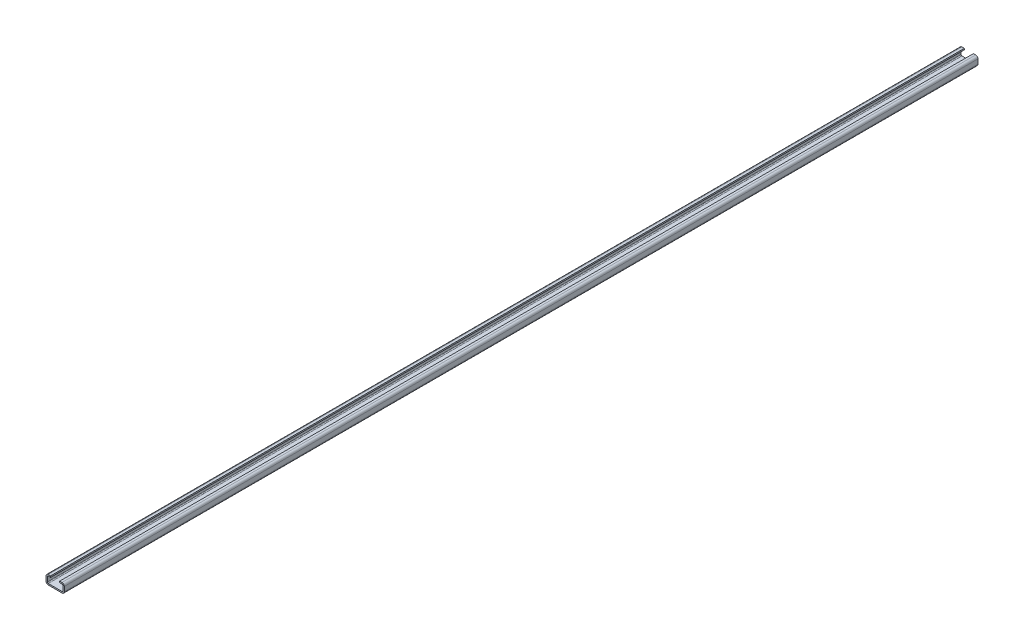
SolidWorks part; units mm, degrees
extrude "Base-Extrude-Thin" add sketch "Sketch1" along normal blind 2000 thin
sketch "Sketch1" plane through (0, 0, 0) normal (0, 0, 1) x (1, 0, 0)
  line L0 (15, 0) -> (-15, 0)
  line L1 (-20, 5) -> (-20, 15)
  line L2 (-15, 20) -> (-10, 20)
  line L3 (0, -23.5917) -> (0, 41.8217) construction
  line L4 (15, 20) -> (10, 20)
  line L5 (20, 5) -> (20, 15)
  arc A0 (-20, 15) -> (-15, 20) centre (-15, 15) cw
  arc A1 (15, 20) -> (20, 15) centre (15, 15) cw
  arc A2 (-20, 5) -> (-15, 0) centre (-15, 5) ccw
  arc A3 (20, 5) -> (15, 0) centre (15, 5) cw
  point P10 (0, 0)
  dimension "D3" = 5
  dimension "D4" = 5
  dimension "D5" = 5
  dimension "D6" = 5
  dimension "D1" = 40
  dimension "D2" = 20
  dimension "D7" = 10
ref_plane "Front" through (0, 0, 0) normal (0, 0, 1) x (1, 0, 0)
ref_plane "Top" through (0, 0, 0) normal (0, 1, 0) x (1, 0, 0)
ref_plane "Right" through (0, 0, 0) normal (1, 0, 0) x (0, 0, -1)
